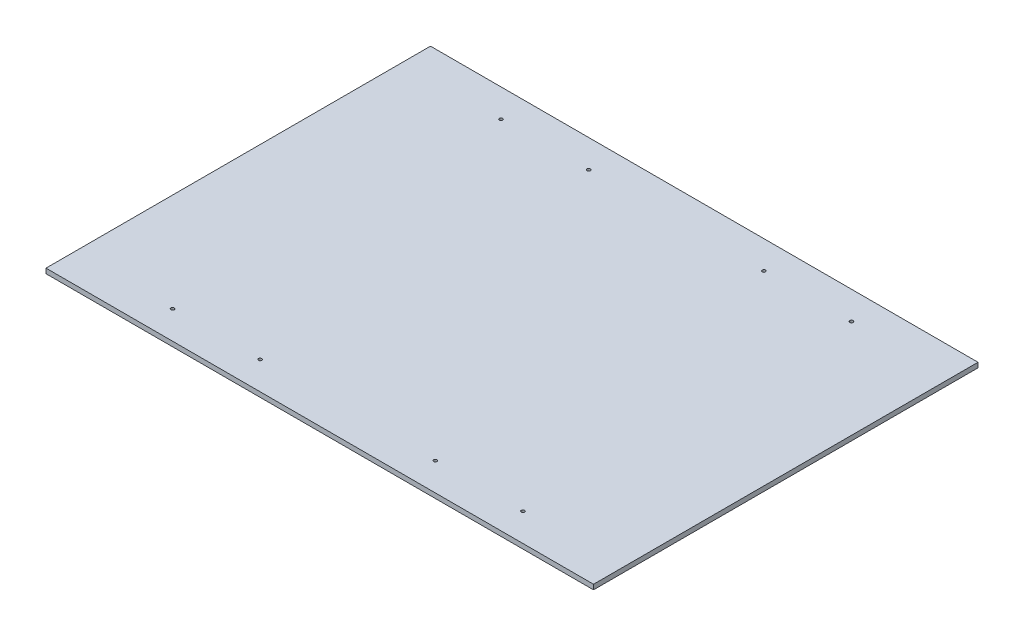
SolidWorks part; units mm, degrees
material "6061-T6 (SS)"
ref_plane "Front Plane" through (0, 0, 0) normal (0, 0, 1) x (1, 0, 0)
ref_plane "Top Plane" through (0, 0, 0) normal (0, 1, 0) x (1, 0, 0)
ref_plane "Right Plane" through (0, 0, 0) normal (1, 0, 0) x (0, 0, -1)
sketch "Sketch1" plane through (0, 0, 0) normal (0, 1, 0) x (1, 0, 0)
  line L1 (-357.1875, -250.825) -> (357.1875, -250.825)
  line L2 (-357.1875, -250.825) -> (-357.1875, 250.825)
  line L3 (-357.1875, 250.825) -> (357.1875, 250.825)
  line L4 (357.1875, -250.825) -> (357.1875, 250.825)
  line L5 (-357.1875, -250.825) -> (357.1875, 250.825) construction
  line L6 (-357.1875, 250.825) -> (357.1875, -250.825) construction
  point P0 (0, 0)
  dimension "D1" = 501.65
  dimension "D2" = 714.375
extrude "Boss-Extrude1" add sketch "Sketch1" along normal blind 6.35
sketch "Sketch2" plane through (0, 6.35, 0) normal (0, 1, 0) x (1, 0, 0)
  line L0 (0, 250.825) -> (0, -250.825) construction
  line L1 (357.1875, 250.825) -> (-357.1875, 250.825) construction
  line L2 (-357.1875, -250.825) -> (357.1875, -250.825) construction
  line L3 (-357.1875, 0) -> (357.1875, 0) construction
  line L4 (-357.1875, 250.825) -> (-357.1875, -250.825) construction
  line L5 (357.1875, -250.825) -> (357.1875, 250.825) construction
  line L6 (-357.1875, -246.0625) -> (357.1875, -246.0625) construction
  line L7 (-357.1875, 246.0625) -> (357.1875, 246.0625) construction
  line L8 (-352.425, 250.825) -> (-352.425, -250.825) construction
  line L9 (352.425, 250.825) -> (352.425, -250.825) construction
  line L10 (-352.425, -182.5625) -> (352.425, -182.5625) construction
  line L11 (0, -182.5625) -> (0, -246.0625) construction
  line L12 (-352.425, -214.3125) -> (0, -214.3125) construction
  line L13 (-114.3, -214.3125) -> (114.3, -214.3125) construction
  line L14 (-228.6, -214.3125) -> (228.6, -214.3125) construction
  line L15 (-228.6, 214.3125) -> (228.6, 214.3125) construction
  line L16 (-114.3, 214.3125) -> (114.3, 214.3125) construction
  line L17 (-352.425, 214.3125) -> (0, 214.3125) construction
  line L18 (0, 182.5625) -> (0, 246.0625) construction
  line L19 (-352.425, 182.5625) -> (352.425, 182.5625) construction
  line L20 (-357.1875, 246.0625) -> (357.1875, 246.0625) construction
  circle A0 centre (-114.3, -214.3125) radius 2.1527
  circle A1 centre (-228.6, -214.3125) radius 2.1527
  circle A2 centre (228.6, -214.3125) radius 2.1527
  circle A3 centre (114.3, -214.3125) radius 2.1527
  circle A4 centre (114.3, 214.3125) radius 2.1527
  circle A5 centre (228.6, 214.3125) radius 2.1527
  circle A6 centre (-228.6, 214.3125) radius 2.1527
  circle A7 centre (-114.3, 214.3125) radius 2.1527
  dimension "D6" = 4.3053
  dimension "D1" = 4.7625
  dimension "D2" = 4.7625
  dimension "D3" = 63.5
  dimension "D4" = 114.3
  dimension "D5" = 228.6
extrude "Cut-Extrude1" cut sketch "Sketch2" against normal through all
sketch "Sketch3" plane through (0, 6.35, 0) normal (0, 1, 0) x (1, 0, 0)
  line L0 (0, 250.825) -> (0, -250.825) construction
  line L1 (357.1875, 250.825) -> (-357.1875, 250.825) construction
  line L2 (-357.1875, -250.825) -> (357.1875, -250.825) construction
  line L3 (-357.1875, 0) -> (357.1875, 0) construction
  line L4 (-357.1875, 250.825) -> (-357.1875, -250.825) construction
  line L5 (357.1875, -250.825) -> (357.1875, 250.825) construction
  line L6 (0, 114.554) -> (357.1875, 114.554) construction
  line L7 (284.6388, 114.554) -> (284.6388, 0) construction
  line L8 (289.56, 0) -> (289.56, -177.8) construction
  line L9 (0, 250.825) -> (357.1875, 250.825) construction
  line L10 (178.5937, 250.825) -> (178.5937, -250.825) construction
  line L11 (289.56, 114.554) -> (289.56, 0) construction
  line L12 (280.9875, 114.554) -> (280.9875, 0) construction
  line L13 (280.9875, 0) -> (280.9875, -177.8) construction
  line L14 (76.2, 0) -> (76.2, -177.8) construction
  line L15 (76.2, 114.554) -> (76.2, 0) construction
  line L16 (67.6275, 114.554) -> (67.6275, 0) construction
  line L17 (67.6275, 0) -> (67.6275, -177.8) construction
  line L18 (72.5487, 114.554) -> (72.5487, 0) construction
  line L19 (-72.5487, 114.554) -> (-72.5487, 0) construction
  line L20 (-67.6275, 0) -> (-67.6275, -177.8) construction
  line L21 (-67.6275, 114.554) -> (-67.6275, 0) construction
  line L22 (-76.2, 114.554) -> (-76.2, 0) construction
  line L23 (-76.2, 0) -> (-76.2, -177.8) construction
  line L24 (-280.9875, 0) -> (-280.9875, -177.8) construction
  line L25 (-280.9875, 114.554) -> (-280.9875, 0) construction
  line L26 (-289.56, 114.554) -> (-289.56, 0) construction
  line L27 (-178.5938, 250.825) -> (-178.5938, -250.825) construction
  line L28 (-289.56, 0) -> (-289.56, -177.8) construction
  line L29 (-284.6388, 114.554) -> (-284.6388, 0) construction
  circle A0 centre (289.56, -152.4) radius 2.1526
  circle A1 centre (76.2, 101.6) radius 2.1526
  circle A2 centre (289.56, -50.8) radius 2.1526
  circle A3 centre (289.56, 50.8) radius 2.1526
  circle A4 centre (289.56, 152.4) radius 2.1526
  circle A5 centre (280.9875, -101.6) radius 2.1526
  circle A6 centre (280.9875, 0) radius 2.1526
  circle A7 centre (280.9875, 101.6) radius 2.1526
  circle A8 centre (76.2, 0) radius 2.1526
  circle A9 centre (76.2, -101.6) radius 2.1526
  circle A10 centre (67.6275, 152.4) radius 2.1526
  circle A11 centre (67.6275, 50.8) radius 2.1526
  circle A12 centre (67.6275, -50.8) radius 2.1526
  circle A13 centre (67.6275, -152.4) radius 2.1526
  circle A14 centre (-67.6275, -152.4) radius 2.1526
  circle A15 centre (-67.6275, -50.8) radius 2.1526
  circle A16 centre (-67.6275, 50.8) radius 2.1526
  circle A17 centre (-67.6275, 152.4) radius 2.1526
  circle A18 centre (-76.2, -101.6) radius 2.1526
  circle A19 centre (-76.2, 0) radius 2.1526
  circle A20 centre (-280.9875, 101.6) radius 2.1526
  circle A21 centre (-280.9875, 0) radius 2.1526
  circle A22 centre (-280.9875, -101.6) radius 2.1526
  circle A23 centre (-289.56, 152.4) radius 2.1526
  circle A24 centre (-289.56, 50.8) radius 2.1526
  circle A25 centre (-289.56, -50.8) radius 2.1526
  circle A26 centre (-76.2, 101.6) radius 2.1526
  circle A27 centre (-289.56, -152.4) radius 2.1526
  dimension "D8" = 101.6
  dimension "D5" = 3.6512
  dimension "D7" = 25.4
  dimension "D6" = 177.8
  dimension "D9" = 50.8
  dimension "D10" = 4.3053
  dimension "D14" = 4.3053
  dimension "D1" = 114.554
  dimension "D2" = 106.045
  dimension "D3" = 177.8
  dimension "D4" = 4.9213
  dimension "D11" = 4
  dimension "D12" = 101.6
  dimension "D13" = 101.6
extrude "Cut-Extrude3" [suppressed] cut sketch "Sketch3" against normal up to next
